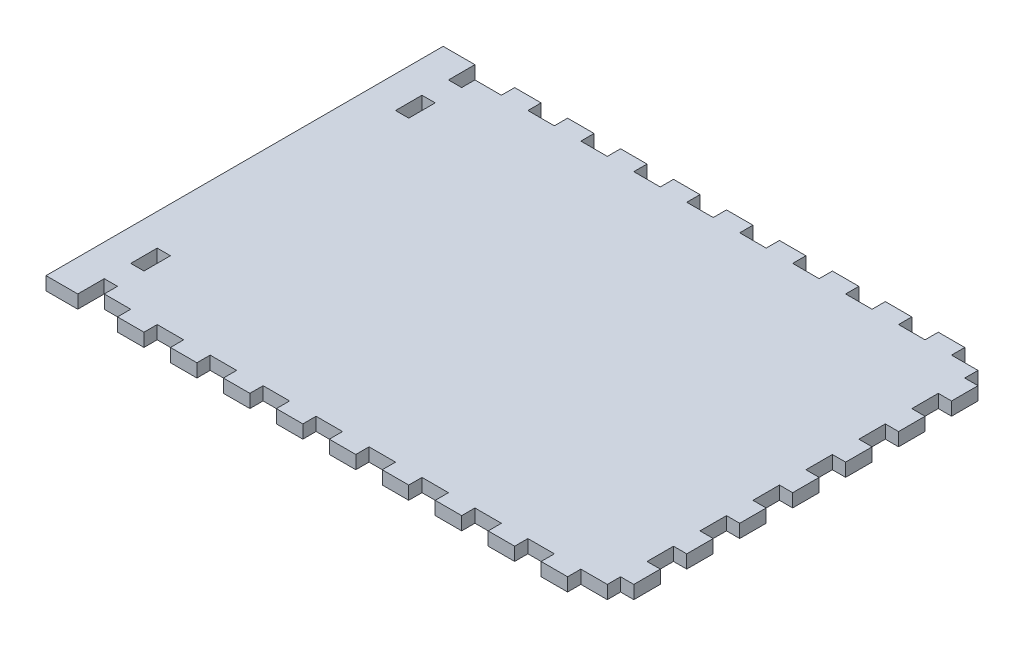
SolidWorks part; units mm, degrees
material "Balsa"
ref_plane "Alzado" through (0, 0, 0) normal (0, 0, 1) x (1, 0, 0)
ref_plane "Planta" through (0, 0, 0) normal (0, 1, 0) x (1, 0, 0)
ref_plane "Vista lateral" through (0, 0, 0) normal (1, 0, 0) x (0, 0, -1)
sketch "Croquis1" plane through (0, 0, 0) normal (0, 1, 0) x (1, 0, 0)
  line L0 (45, 0) -> (45, 5)
  line L1 (0, 0) -> (200, 0)
  line L2 (0, 0) -> (0, 150)
  line L3 (0, 150) -> (200, 150)
  line L4 (200, 0) -> (200, 150)
  line L5 (0, 0) -> (15, 0)
  line L6 (0, 0) -> (0, 5)
  line L7 (0, 5) -> (15, 5)
  line L8 (15, 0) -> (15, 5)
  line L9 (25, 0) -> (35, 0)
  line L10 (25, 0) -> (25, 5)
  line L11 (25, 5) -> (35, 5)
  line L12 (35, 0) -> (35, 5)
  line L13 (45, 0) -> (55, 0)
  line L14 (55, 0) -> (55, 5)
  line L15 (45, 5) -> (55, 5)
  line L16 (65, 0) -> (65, 5)
  line L17 (65, 0) -> (75, 0)
  line L18 (75, 0) -> (75, 5)
  line L19 (65, 5) -> (75, 5)
  line L20 (85, 0) -> (85, 5)
  line L21 (85, 0) -> (95, 0)
  line L22 (95, 0) -> (95, 5)
  line L23 (85, 5) -> (95, 5)
  line L24 (105, 0) -> (105, 5)
  line L25 (105, 0) -> (115, 0)
  line L26 (115, 0) -> (115, 5)
  line L27 (105, 5) -> (115, 5)
  line L28 (125, 0) -> (125, 5)
  line L29 (125, 0) -> (135, 0)
  line L30 (135, 0) -> (135, 5)
  line L31 (125, 5) -> (135, 5)
  line L32 (145, 0) -> (145, 5)
  line L33 (145, 0) -> (155, 0)
  line L34 (155, 0) -> (155, 5)
  line L35 (145, 5) -> (155, 5)
  line L36 (165, 0) -> (165, 5)
  line L37 (165, 0) -> (175, 0)
  line L38 (175, 0) -> (175, 5)
  line L39 (165, 5) -> (175, 5)
  line L40 (0, 130) -> (0, 120)
  line L41 (200, 5) -> (185, 5)
  line L42 (185, 0) -> (185, 5)
  line L43 (200, 0) -> (185, 0)
  line L44 (200, 0) -> (200, 5)
  line L45 (0, 145) -> (15, 145)
  line L46 (15, 150) -> (15, 145)
  line L47 (0, 150) -> (15, 150)
  line L48 (0, 150) -> (0, 145)
  line L49 (25, 145) -> (35, 145)
  line L50 (35, 150) -> (35, 145)
  line L51 (25, 150) -> (35, 150)
  line L52 (25, 150) -> (25, 145)
  line L53 (45, 150) -> (55, 150)
  line L54 (55, 150) -> (55, 145)
  line L55 (45, 145) -> (55, 145)
  line L56 (45, 150) -> (45, 145)
  line L57 (65, 150) -> (75, 150)
  line L58 (75, 150) -> (75, 145)
  line L59 (65, 145) -> (75, 145)
  line L60 (65, 150) -> (65, 145)
  line L61 (85, 150) -> (95, 150)
  line L62 (95, 150) -> (95, 145)
  line L63 (85, 145) -> (95, 145)
  line L64 (85, 150) -> (85, 145)
  line L65 (105, 150) -> (115, 150)
  line L66 (115, 150) -> (115, 145)
  line L67 (105, 145) -> (115, 145)
  line L68 (105, 150) -> (105, 145)
  line L69 (125, 150) -> (135, 150)
  line L70 (135, 150) -> (135, 145)
  line L71 (125, 145) -> (135, 145)
  line L72 (125, 150) -> (125, 145)
  line L73 (145, 150) -> (155, 150)
  line L74 (155, 150) -> (155, 145)
  line L75 (145, 145) -> (155, 145)
  line L76 (145, 150) -> (145, 145)
  line L77 (165, 150) -> (175, 150)
  line L78 (175, 150) -> (175, 145)
  line L79 (165, 145) -> (175, 145)
  line L80 (165, 150) -> (165, 145)
  line L81 (200, 150) -> (185, 150)
  line L82 (185, 150) -> (185, 145)
  line L83 (200, 145) -> (185, 145)
  line L84 (200, 150) -> (200, 145)
  line L85 (0, 150) -> (5, 150)
  line L86 (0, 150) -> (0, 140)
  line L87 (0, 140) -> (5, 140)
  line L88 (5, 150) -> (5, 140)
  line L89 (0, 130) -> (5, 130)
  line L90 (5, 130) -> (5, 120)
  line L91 (0, 120) -> (5, 120)
  line L108 (0, 30) -> (0, 20)
  line L109 (0, 30) -> (5, 30)
  line L110 (5, 30) -> (5, 20)
  line L111 (0, 20) -> (5, 20)
  line L112 (0, 10) -> (0, 0)
  line L113 (0, 10) -> (5, 10)
  line L114 (5, 10) -> (5, 0)
  line L115 (0, 0) -> (5, 0)
  line L117 (200, 10) -> (195, 10)
  line L118 (195, 10) -> (195, 0)
  line L119 (200, 0) -> (195, 0)
  line L120 (200, 10) -> (200, 0)
  line L121 (200, 30) -> (195, 30)
  line L122 (195, 30) -> (195, 20)
  line L123 (200, 20) -> (195, 20)
  line L124 (200, 30) -> (200, 20)
  line L125 (200, 50) -> (195, 50)
  line L126 (195, 50) -> (195, 40)
  line L127 (200, 40) -> (195, 40)
  line L128 (200, 50) -> (200, 40)
  line L129 (200, 70) -> (195, 70)
  line L130 (195, 70) -> (195, 60)
  line L131 (200, 60) -> (195, 60)
  line L132 (200, 70) -> (200, 60)
  line L133 (200, 90) -> (195, 90)
  line L134 (195, 90) -> (195, 80)
  line L135 (200, 80) -> (195, 80)
  line L136 (200, 90) -> (200, 80)
  line L137 (200, 110) -> (195, 110)
  line L138 (195, 110) -> (195, 100)
  line L139 (200, 100) -> (195, 100)
  line L140 (200, 110) -> (200, 100)
  line L141 (200, 130) -> (195, 130)
  line L142 (195, 130) -> (195, 120)
  line L143 (200, 120) -> (195, 120)
  line L144 (200, 130) -> (200, 120)
  line L145 (200, 140) -> (195, 140)
  line L146 (195, 150) -> (195, 140)
  line L147 (200, 150) -> (195, 150)
  line L148 (200, 150) -> (200, 140)
  line L149 (0, 110) -> (0, 100) [skipped]
  line L150 (0, 100) -> (5, 100) [skipped]
  line L151 (5, 110) -> (5, 100) [skipped]
  line L152 (0, 110) -> (5, 110) [skipped]
  line L153 (0, 90) -> (0, 80) [skipped]
  line L154 (0, 80) -> (5, 80) [skipped]
  line L155 (5, 90) -> (5, 80) [skipped]
  line L156 (0, 90) -> (5, 90) [skipped]
  line L157 (0, 70) -> (0, 60) [skipped]
  line L158 (0, 60) -> (5, 60) [skipped]
  line L159 (5, 70) -> (5, 60) [skipped]
  line L160 (0, 70) -> (5, 70) [skipped]
  line L161 (0, 50) -> (0, 40) [skipped]
  line L162 (0, 40) -> (5, 40) [skipped]
  line L163 (5, 50) -> (5, 40) [skipped]
  line L164 (0, 50) -> (5, 50) [skipped]
  dimension "D1" = 200
  dimension "D2" = 150
  dimension "D3" = 15
  dimension "D4" = 5
  dimension "D5" = 10
  dimension "D6" = 10
  dimension "D7" = 5
  dimension "D9" = 10
  dimension "D10" = 5
  dimension "D8" = 8
  dimension "D11" = 8
extrude "Saliente-Extruir1" add sketch "Croquis1" along normal blind 5
sketch "Croquis2" plane through (0, 5, 0) normal (0, 1, 0) x (1, 0, 0)
  line L1 (-12, 0) -> (0, 0)
  line L2 (-12, 0) -> (-12, 150)
  line L3 (-12, 150) -> (0, 150)
  line L4 (0, 0) -> (0, 150)
  line L5 (0, 30) -> (0, 120) construction
  dimension "D1" = 150
  dimension "D2" = 12
  dimension "D3" = 0
extrude "Saliente-Extruir3" add sketch "Croquis2" against normal blind 5
